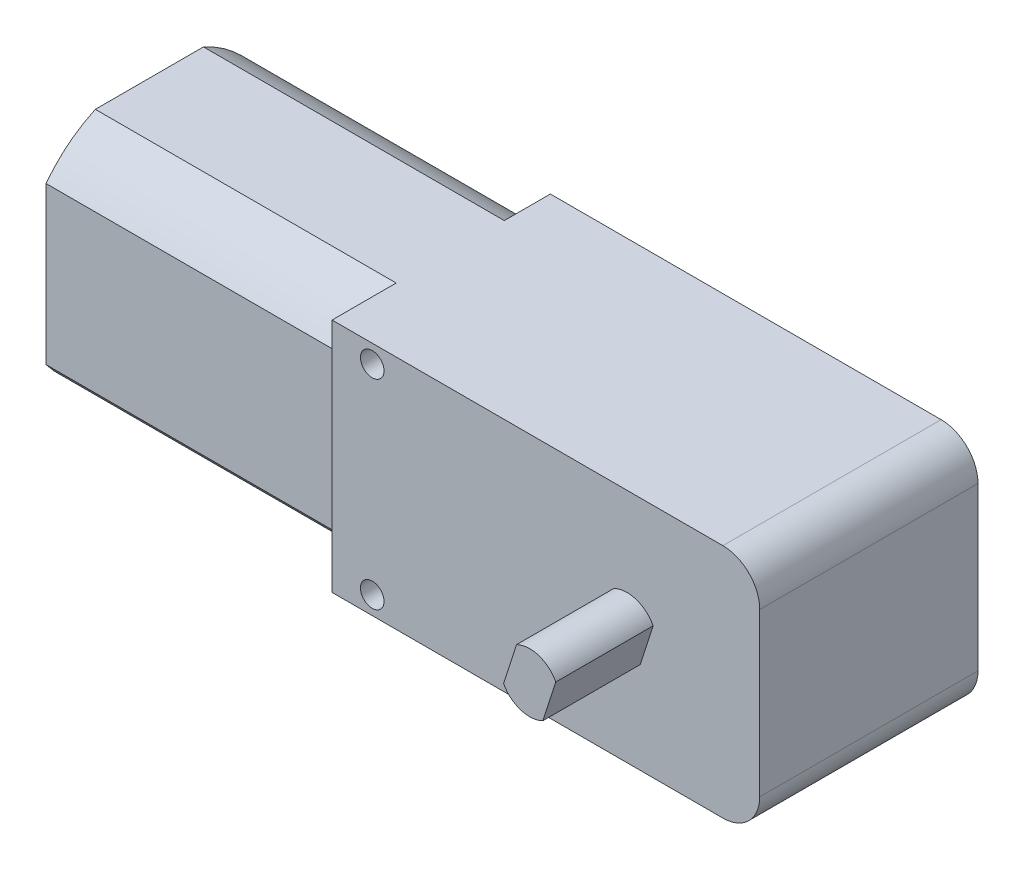
SolidWorks part; units mm, degrees
ref_plane "Front Plane" through (0, 0, 0) normal (0, 0, 1) x (1, 0, 0)
ref_plane "Top Plane" through (0, 0, 0) normal (0, 1, 0) x (1, 0, 0)
ref_plane "Right Plane" through (0, 0, 0) normal (1, 0, 0) x (0, 0, -1)
sketch "Sketch1" plane through (0, 0, 0) normal (0, 0, 1) x (1, 0, 0)
  line L1 (0, -10.16) -> (36.83, -10.16)
  line L2 (0, -10.16) -> (0, 10.16)
  line L3 (0, 10.16) -> (36.83, 10.16)
  line L4 (36.83, -10.16) -> (36.83, 10.16)
  point P4 (0, 0)
  dimension "D1" = 36.83
  dimension "D2" = 20.32
extrude "Boss-Extrude1" add sketch "Sketch1" along normal blind 18.796
fillet "Fillet1" radius 3.175 2 edges at (36.83, 10.16, 9.398) (36.83, -10.16, 9.398)
sketch "Sketch2" plane through (0, 0, 0) normal (-1, 0, 0) x (0, 0, 1)
  line L0 (0, 7.112) -> (0, -7.112)
  line L1 (0, 10.16) -> (0, -10.16) construction
  line L2 (17.526, -6.7531) -> (17.526, 6.7531)
  line L3 (18.796, 10.16) -> (18.796, -10.16) construction
  line L6 (0, 10.16) -> (0, -10.16)
  line L7 (0, -10.16) -> (18.796, -10.16)
  line L8 (18.796, -10.16) -> (18.796, 10.16)
  line L9 (18.796, 10.16) -> (0, 10.16)
  line L10 (0, 7.112) -> (0, -7.112)
  line L11 (3.9651, -10.16) -> (13.2769, -10.16)
  line L13 (13.2769, 10.16) -> (3.9651, 10.16)
  arc A0 (3.9651, 10.16) -> (0, 7.112) centre (8.621, 0) ccw
  arc A1 (13.2769, -10.16) -> (17.526, -6.7531) centre (8.621, 0) ccw
  arc A2 (0, -7.112) -> (3.9651, -10.16) centre (8.621, 0) ccw
  arc A3 (17.526, 6.7531) -> (13.2769, 10.16) centre (8.621, 0) ccw
  line M3 (0, 10.16) -> (0, -10.16)
  line M4 (0, -10.16) -> (18.796, -10.16)
  line M6 (18.796, 10.16) -> (0, 10.16)
  dimension "D1" = 22.352
  dimension "D2" = 14.224
  dimension "D4" = 1.27
  dimension "D3" = 0
extrude "Boss-Extrude2" add sketch "Sketch2" along normal blind 25.908 contours L2 A3 A0 A2 A1 M6 M3 M4
sketch "Sketch3" plane through (0, 0, 18.796) normal (0, 0, 1) x (1, 0, 0)
  line L0 (36.83, -6.985) -> (36.83, 6.985) construction
  line L1 (23.7085, 0.5477) -> (27.0915, -0.5477) construction
  line L2 (24.2673, 2.2734) -> (23.1497, -1.178)
  line L3 (27.6503, 1.178) -> (26.5327, -2.2734)
  arc A0 (23.1497, -1.178) -> (26.5327, -2.2734) centre (25.4, 0) ccw
  arc A1 (27.6503, 1.178) -> (24.2673, 2.2734) centre (25.4, 0) ccw
  point P7 (25.4, 0)
  point P11 (0, 0)
  point P12 (0, 0)
  dimension "D2" = 5.08
  dimension "D1" = 11.43
  dimension "D3" = 3.556
extrude "Boss-Extrude3" add sketch "Sketch3" along normal blind 8.382
sketch "Sketch4" plane through (0, 0, 18.796) normal (0, 0, 1) x (1, 0, 0)
  line L0 (14.9479, 0) -> (-14.9479, 0) construction
  circle A0 centre (3.4562, 8.5975) radius 1.016
  circle A1 centre (3.4562, -8.5975) radius 1.016
  point P6 (3.4562, 8.5975)
  dimension "D1" = 2.032
extrude "Cut-Extrude1" cut sketch "Sketch4" against normal through all
